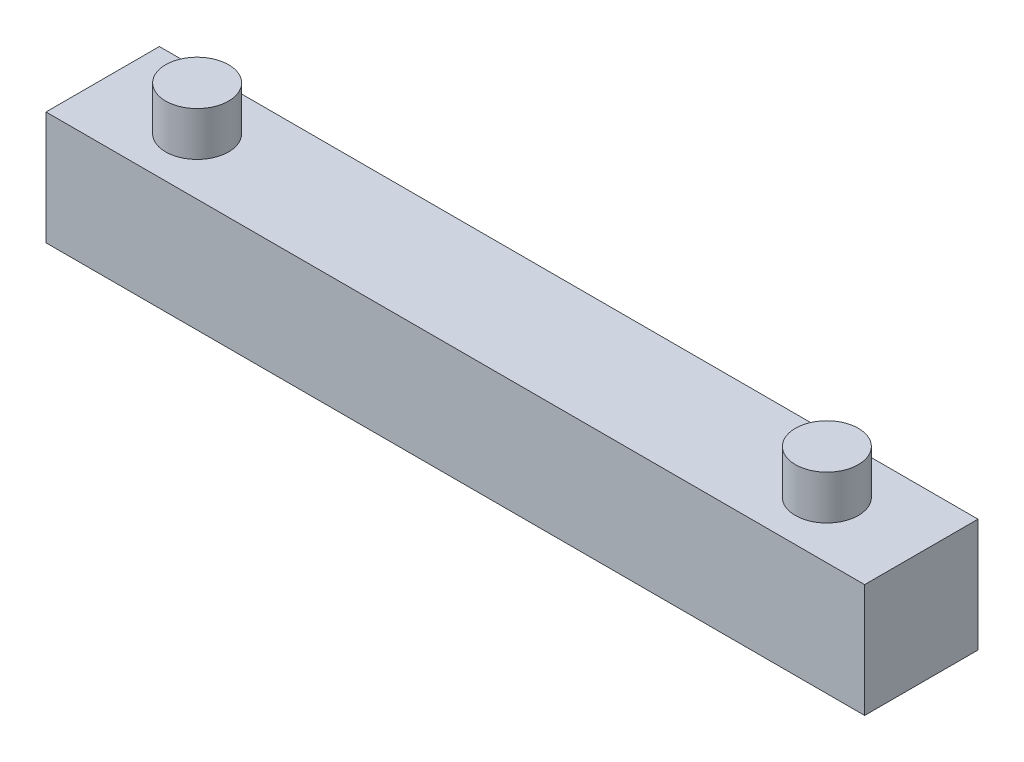
SolidWorks part; units mm, degrees
ref_plane "Front Plane" through (0, 0, 0) normal (0, 0, 1) x (1, 0, 0)
ref_plane "Top Plane" through (0, 0, 0) normal (0, 1, 0) x (1, 0, 0)
ref_plane "Right Plane" through (0, 0, 0) normal (1, 0, 0) x (0, 0, -1)
sketch "Sketch1" plane through (0, 0, 0) normal (0, 1, 0) x (1, 0, 0)
  line L1 (0, 0) -> (65, 0)
  line L2 (0, 0) -> (0, -9)
  line L3 (0, -9) -> (65, -9)
  line L4 (65, 0) -> (65, -9)
  dimension "D1" = 9
  dimension "D2" = 65
extrude "Boss-Extrude1" add sketch "Sketch1" along normal blind 9
sketch "Sketch2" plane through (0, 9, 0) normal (0, 1, 0) x (1, 0, 0)
  circle A0 centre (7.5, -4.5) radius 2.5
  circle A1 centre (57.5, -4.5) radius 2.5
  dimension "D1" = 5
  dimension "D2" = 5
extrude "Boss-Extrude2" add sketch "Sketch2" along normal blind 3.5
